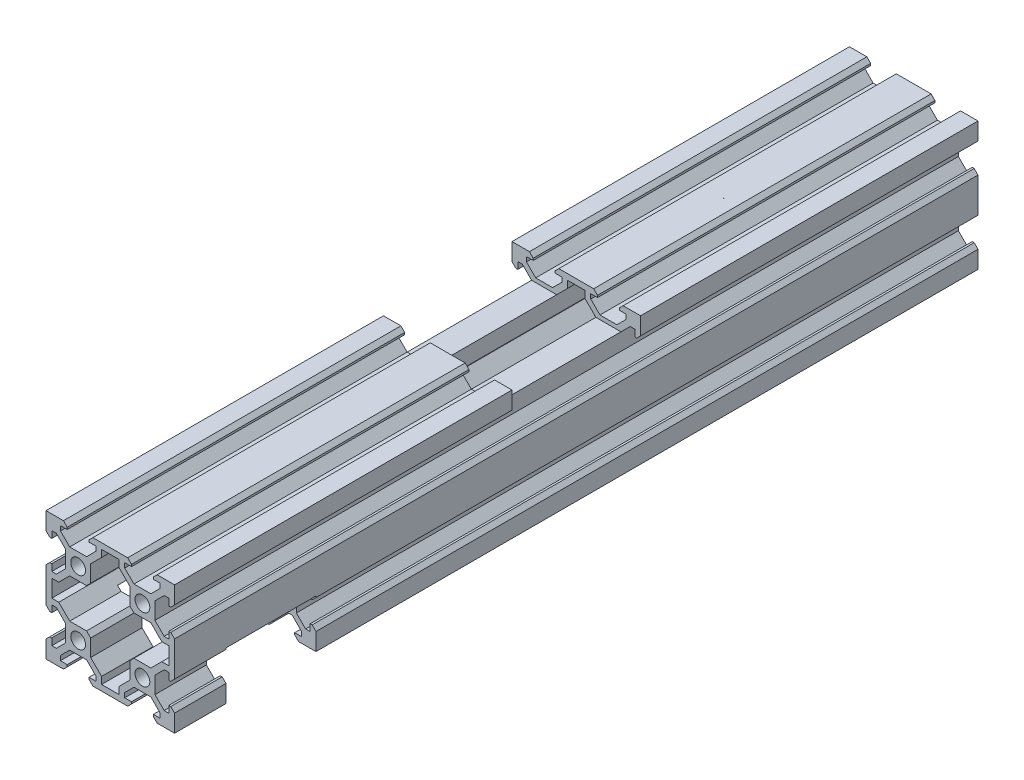
SolidWorks part; units mm, degrees
ref_plane "Front Plane" through (0, 0, 0) normal (0, 0, 1) x (1, 0, 0)
ref_plane "Top Plane" through (0, 0, 0) normal (0, 1, 0) x (1, 0, 0)
ref_plane "Right Plane" through (0, 0, 0) normal (1, 0, 0) x (0, 0, -1)
sketch "Sketch1" plane through (0, 0, 0) normal (0, 0, 1) x (1, 0, 0)
  line L1 (0, 0) -> (40, 0)
  line L2 (0, 0) -> (0, 40)
  line L3 (0, 40) -> (40, 40)
  line L4 (40, 0) -> (40, 40)
  dimension "D1" = 40
extrude "Boss-Extrude1" add sketch "Sketch1" against normal blind 250
sketch "Sketch2" plane through (0, 0, 0) normal (0, 0, 1) x (1, 0, 0)
  line L0 (0, 20) -> (40, 20) construction
  line L1 (0, 40) -> (0, 0) construction
  line L2 (40, 0) -> (40, 40) construction
  line L3 (20, 40) -> (20, 0) construction
  line L4 (40, 40) -> (0, 40) construction
  line L5 (0, 0) -> (40, 0) construction
  line L6 (6.605, 38.815) -> (6.605, 38.2)
  line L7 (6.605, 38.2) -> (4.5, 38.2)
  line L8 (4.5, 38.2) -> (4.5, 36.7728)
  line L9 (4.5, 36.7728) -> (7.3728, 33.9)
  line L10 (7.3728, 33.9) -> (12.6272, 33.9)
  line L11 (12.6272, 33.9) -> (15.5, 36.7728)
  line L12 (15.5, 36.7728) -> (15.5, 38.2)
  line L13 (15.5, 38.2) -> (13.395, 38.2)
  line L14 (13.395, 38.2) -> (13.395, 38.815)
  line L16 (6.605, 38.815) -> (5.42, 40)
  line L17 (13.395, 38.815) -> (14.58, 40)
  line L18 (14.58, 40) -> (5.42, 40)
  line L19 (26.605, 38.815) -> (25.42, 40)
  line L20 (26.605, 38.2) -> (26.605, 38.815)
  line L21 (24.5, 38.2) -> (26.605, 38.2)
  line L22 (24.5, 36.7728) -> (24.5, 38.2)
  line L23 (27.3728, 33.9) -> (24.5, 36.7728)
  line L24 (32.6272, 33.9) -> (27.3728, 33.9)
  line L25 (35.5, 36.7728) -> (32.6272, 33.9)
  line L26 (35.5, 38.2) -> (35.5, 36.7728)
  line L27 (33.395, 38.2) -> (35.5, 38.2)
  line L28 (33.395, 38.815) -> (33.395, 38.2)
  line L29 (33.395, 38.815) -> (34.58, 40)
  line L30 (25.42, 40) -> (34.58, 40)
  line L31 (26.605, 1.8) -> (26.605, 1.185)
  line L32 (24.5, 1.8) -> (26.605, 1.8)
  line L33 (24.5, 3.2272) -> (24.5, 1.8)
  line L34 (27.3728, 6.1) -> (24.5, 3.2272)
  line L35 (32.6272, 6.1) -> (27.3728, 6.1)
  line L36 (35.5, 3.2272) -> (32.6272, 6.1)
  line L37 (35.5, 1.8) -> (35.5, 3.2272)
  line L38 (33.395, 1.8) -> (35.5, 1.8)
  line L39 (33.395, 1.185) -> (33.395, 1.8)
  line L40 (33.395, 1.185) -> (34.58, 0)
  line L41 (25.42, 0) -> (34.58, 0)
  line L42 (26.605, 1.185) -> (25.42, 0)
  line L43 (13.395, 1.185) -> (14.58, 0)
  line L44 (13.395, 1.8) -> (13.395, 1.185)
  line L45 (15.5, 1.8) -> (13.395, 1.8)
  line L46 (15.5, 3.2272) -> (15.5, 1.8)
  line L47 (12.6272, 6.1) -> (15.5, 3.2272)
  line L48 (7.3728, 6.1) -> (12.6272, 6.1)
  line L49 (4.5, 3.2272) -> (7.3728, 6.1)
  line L50 (4.5, 1.8) -> (4.5, 3.2272)
  line L51 (6.605, 1.8) -> (4.5, 1.8)
  line L52 (6.605, 1.185) -> (6.605, 1.8)
  line L53 (6.605, 1.185) -> (5.42, 0)
  line L54 (14.58, 0) -> (5.42, 0)
  line L55 (0, 0) -> (40, 40) construction
  line L56 (1.8, 13.395) -> (1.185, 13.395)
  line L57 (1.8, 15.5) -> (1.8, 13.395)
  line L58 (3.2272, 15.5) -> (1.8, 15.5)
  line L59 (6.1, 12.6272) -> (3.2272, 15.5)
  line L60 (6.1, 7.3728) -> (6.1, 12.6272)
  line L61 (3.2272, 4.5) -> (6.1, 7.3728)
  line L62 (1.8, 4.5) -> (3.2272, 4.5)
  line L63 (1.8, 6.605) -> (1.8, 4.5)
  line L64 (1.185, 6.605) -> (1.8, 6.605)
  line L65 (1.185, 6.605) -> (0, 5.42)
  line L66 (0, 14.58) -> (0, 5.42)
  line L67 (1.185, 13.395) -> (0, 14.58)
  line L68 (0, 40) -> (40, 0) construction
  line L69 (1.185, 26.605) -> (0, 25.42)
  line L70 (1.8, 26.605) -> (1.185, 26.605)
  line L71 (1.8, 24.5) -> (1.8, 26.605)
  line L72 (3.2272, 24.5) -> (1.8, 24.5)
  line L73 (6.1, 27.3728) -> (3.2272, 24.5)
  line L74 (6.1, 32.6272) -> (6.1, 27.3728)
  line L75 (3.2272, 35.5) -> (6.1, 32.6272)
  line L76 (1.8, 35.5) -> (3.2272, 35.5)
  line L77 (1.8, 33.395) -> (1.8, 35.5)
  line L78 (1.185, 33.395) -> (1.8, 33.395)
  line L79 (1.185, 33.395) -> (0, 34.58)
  line L80 (0, 25.42) -> (0, 34.58)
  line L81 (38.2, 15.5) -> (38.2, 13.395)
  line L82 (36.7728, 15.5) -> (38.2, 15.5)
  line L83 (33.9, 12.6272) -> (36.7728, 15.5)
  line L84 (33.9, 7.3728) -> (33.9, 12.6272)
  line L85 (36.7728, 4.5) -> (33.9, 7.3728)
  line L86 (38.2, 4.5) -> (36.7728, 4.5)
  line L87 (38.2, 6.605) -> (38.2, 4.5)
  line L88 (38.815, 6.605) -> (38.2, 6.605)
  line L89 (38.815, 6.605) -> (40, 5.42)
  line L90 (40, 14.58) -> (40, 5.42)
  line L91 (38.815, 13.395) -> (40, 14.58)
  line L92 (38.2, 13.395) -> (38.815, 13.395)
  line L93 (38.2, 26.605) -> (38.815, 26.605)
  line L94 (38.2, 24.5) -> (38.2, 26.605)
  line L95 (36.7728, 24.5) -> (38.2, 24.5)
  line L96 (33.9, 27.3728) -> (36.7728, 24.5)
  line L97 (33.9, 32.6272) -> (33.9, 27.3728)
  line L98 (36.7728, 35.5) -> (33.9, 32.6272)
  line L99 (38.2, 35.5) -> (36.7728, 35.5)
  line L100 (38.2, 33.395) -> (38.2, 35.5)
  line L101 (38.815, 33.395) -> (38.2, 33.395)
  line L102 (38.815, 33.395) -> (40, 34.58)
  line L103 (40, 25.42) -> (40, 34.58)
  line L104 (38.815, 26.605) -> (40, 25.42)
  circle A0 centre (10, 30) radius 2.3
  circle A2 centre (30, 30) radius 2.3
  circle A3 centre (30, 10) radius 2.3
  circle A4 centre (10, 10) radius 2.3
  point P22 (10, 40)
  point P33 (10, 33.9)
  dimension "D1" = 4.6
  dimension "D2" = 20
  dimension "D3" = 20
  dimension "D4" = 4.3
  dimension "D5" = 6.79
  dimension "D6" = 9.16
  dimension "D7" = 11
  dimension "D8" = 90
  dimension "D9" = 1.8
  dimension "D10" = 1.8
extrude "Cut-Extrude1" cut sketch "Sketch2" against normal up to surface (250 mm away) up to face at (20, 20, -250)
sketch "Sketch3" plane through (0, 0, 0) normal (0, 0, 1) x (1, 0, 0)
  line L0 (17.3, 38.2) -> (22.7, 38.2)
  line L1 (0, 20) -> (40, 20) construction
  line L2 (0, 25.42) -> (0, 14.58) construction
  line L3 (40, 14.58) -> (40, 25.42) construction
  line L4 (1.8, 22.7) -> (1.8, 17.3)
  line L5 (12.6272, 13.9) -> (13.9, 12.6272)
  line L6 (13.9, 12.6272) -> (13.9, 7.3728)
  line L7 (7.3728, 13.9) -> (12.6272, 13.9)
  line L8 (13.9, 7.3728) -> (17.3, 3.9728)
  line L9 (17.3, 3.9728) -> (17.3, 1.8)
  line L10 (1.8, 17.3) -> (3.9728, 17.3)
  line L11 (3.9728, 17.3) -> (7.3728, 13.9)
  line L12 (17.3, 1.8) -> (22.7, 1.8)
  line L13 (27.3728, 26.1) -> (26.1, 27.3728)
  line L14 (26.1, 27.3728) -> (26.1, 32.6272)
  line L15 (32.6272, 26.1) -> (27.3728, 26.1)
  line L16 (26.1, 32.6272) -> (22.7, 36.0272)
  line L17 (22.7, 36.0272) -> (22.7, 38.2)
  line L18 (38.2, 22.7) -> (36.0272, 22.7)
  line L19 (36.0272, 22.7) -> (32.6272, 26.1)
  line L20 (36.0272, 17.3) -> (32.6272, 13.9)
  line L21 (38.2, 17.3) -> (36.0272, 17.3)
  line L22 (22.7, 3.9728) -> (22.7, 1.8)
  line L23 (26.1, 7.3728) -> (22.7, 3.9728)
  line L24 (32.6272, 13.9) -> (27.3728, 13.9)
  line L25 (26.1, 12.6272) -> (26.1, 7.3728)
  line L26 (27.3728, 13.9) -> (26.1, 12.6272)
  line L27 (38.2, 22.7) -> (38.2, 17.3)
  line L117 (3.9728, 22.7) -> (7.3728, 26.1)
  line L118 (1.8, 22.7) -> (3.9728, 22.7)
  line L119 (3.9728, 22.7) -> (7.3728, 26.1)
  line L120 (1.8, 22.7) -> (3.9728, 22.7)
  line L134 (20, 40) -> (20, 0) construction
  line L135 (25.42, 40) -> (14.58, 40) construction
  line L136 (17.3, 36.0272) -> (17.3, 38.2)
  line L137 (13.9, 32.6272) -> (17.3, 36.0272)
  line L138 (17.3, 36.0272) -> (17.3, 38.2)
  line L139 (13.9, 32.6272) -> (17.3, 36.0272)
  line L140 (14.58, 0) -> (25.42, 0) construction
  line L141 (7.3728, 26.1) -> (12.6272, 26.1)
  line L142 (13.9, 27.3728) -> (13.9, 32.6272)
  line L155 (12.6272, 26.1) -> (13.9, 27.3728)
  circle A2 centre (10, 30) radius 2.3 construction
  circle A3 centre (10, 30) radius 2.3 construction
  circle A4 centre (10, 10) radius 2.3 construction
  circle A5 centre (30, 10) radius 2.3 construction
  circle A6 centre (30, 30) radius 2.3 construction
  point P24 (10, 26.1)
  point P25 (38.2, 20)
  point P38 (1.8, 20)
  point P52 (20, 1.8)
  point P59 (20, 38.2)
  dimension "D5" = 135
  dimension "D1" = 1.8
  dimension "D3" = 1.8
extrude "Cut-Extrude2" cut sketch "Sketch3" against normal up to surface (250 mm away) up to face at (20, 20, -250)
sketch "Sketch4" plane through (40, 0, 0) normal (1, 0, 0) x (0, 0, -1)
  line L0 (250, 40) -> (0, 40) construction
  line L1 (105, 40) -> (145, 40)
  line L2 (105, 40) -> (105, 32.6272)
  line L3 (105, 32.6272) -> (145, 32.6272)
  line L4 (145, 40) -> (145, 32.6272)
  line L6 (250, 32.6272) -> (0, 32.6272) construction
  point P9 (125, 40)
  point P10 (125, 40)
  dimension "D1" = 40
extrude "Cut-Extrude3" cut sketch "Sketch4" against normal through all
sketch "Sketch5" plane through (0, 0, 0) normal (-1, 0, 0) x (0, 0, 1)
  line L0 (-250, 0) -> (0, 0) construction
  line L1 (-44, 0) -> (-16, 0)
  line L2 (-44, 0) -> (-44, 15)
  line L3 (-44, 15) -> (-16, 15)
  line L4 (-16, 0) -> (-16, 15)
  line L6 (0, 7.3728) -> (0, 12.6272) construction
  dimension "D1" = 16
  dimension "D2" = 28
  dimension "D3" = 15
extrude "cable gap" cut sketch "Sketch5" against normal up to surface (40 mm away) up to face at (40, 20, -125)
